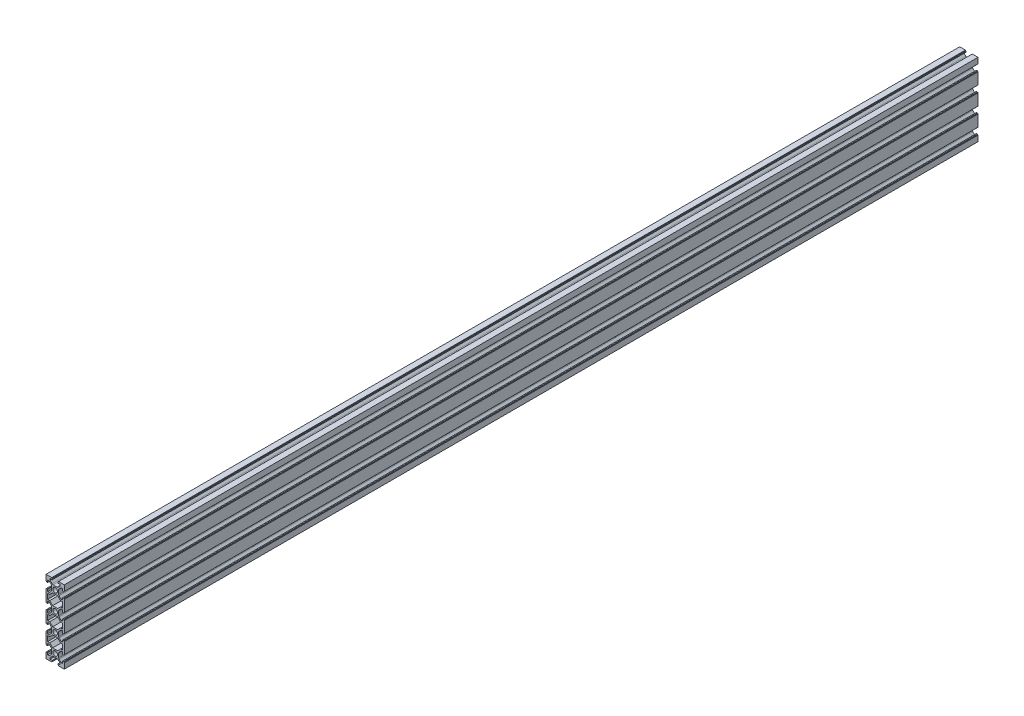
SolidWorks part; units mm, degrees
material "6063 T5"
ref_plane "Спереди" through (0, 0, 0) normal (0, 0, 1) x (1, 0, 0)
ref_plane "Сверху" through (0, 0, 0) normal (0, 1, 0) x (1, 0, 0)
ref_plane "Справа" through (0, 0, 0) normal (1, 0, 0) x (0, 0, -1)
sketch "Эскиз3" plane through (0, 0, 0) normal (0, 0, 1) x (1, 0, 0)
  line L0 (10, 0) -> (10, -20) construction
  line L5 (-10, -5.5) -> (-10, -14.5)
  line L7 (-9.9529, 9.1691) -> (10.0471, 9.1691) construction
  line L8 (-10, 5.5) -> (-10, 10)
  line L9 (-10, 10) -> (-5.5, 10)
  line L10 (5.5, 10) -> (10, 10)
  line L11 (10, 10) -> (10, 5.5)
  line L12 (10, -5.5) -> (10, -14.5)
  line L13 (10, -25.5) -> (10, -34.5)
  line L14 (10, -45.5) -> (10, -54.5)
  line L15 (-10, -25.5) -> (-10, -34.5)
  line L16 (-10, -45.5) -> (-10, -54.5)
  line L17 (-10, -65.5) -> (-10, -70)
  line L18 (-10, -70) -> (-5.5, -70)
  line L20 (5.5, -70) -> (10, -70)
  line L21 (10, -70) -> (10, -65.5)
  line L23 (0, 0) -> (0, -10) construction
  line L24 (0, -10) -> (-10, -10) construction
  line L26 (2.7373, -3.9) -> (-2.7373, -3.9)
  line L27 (-2.7373, -3.9) -> (-5.9373, -7.1)
  line L28 (-5.9373, -7.1) -> (-8.2, -7.1)
  line L29 (-8.2, -7.1) -> (-8.2, -12.9)
  line L31 (5.9373, -7.1) -> (8.2, -7.1)
  line L32 (8.2, -7.1) -> (8.2, -12.9)
  line L33 (2.7373, -3.9) -> (5.9373, -7.1)
  line L35 (-5.9373, -12.9) -> (-8.2, -12.9)
  line L36 (-2.7373, -16.1) -> (-5.9373, -12.9)
  line L37 (2.7373, -16.1) -> (-2.7373, -16.1)
  line L38 (2.7373, -16.1) -> (5.9373, -12.9)
  line L39 (5.9373, -12.9) -> (8.2, -12.9)
  line L41 (-8.2, -27.1) -> (-8.2, -32.9)
  line L42 (-5.9373, -32.9) -> (-8.2, -32.9)
  line L43 (-2.7373, -36.1) -> (-5.9373, -32.9)
  line L44 (2.7373, -36.1) -> (-2.7373, -36.1)
  line L45 (2.7373, -36.1) -> (5.9373, -32.9)
  line L46 (5.9373, -32.9) -> (8.2, -32.9)
  line L47 (8.2, -27.1) -> (8.2, -32.9)
  line L48 (5.9373, -27.1) -> (8.2, -27.1)
  line L49 (2.7373, -23.9) -> (5.9373, -27.1)
  line L50 (2.7373, -23.9) -> (-2.7373, -23.9)
  line L51 (-2.7373, -23.9) -> (-5.9373, -27.1)
  line L52 (-5.9373, -27.1) -> (-8.2, -27.1)
  line L53 (-8.2, -47.1) -> (-8.2, -52.9)
  line L54 (-5.9373, -52.9) -> (-8.2, -52.9)
  line L55 (-2.7373, -56.1) -> (-5.9373, -52.9)
  line L56 (2.7373, -56.1) -> (-2.7373, -56.1)
  line L57 (2.7373, -56.1) -> (5.9373, -52.9)
  line L58 (5.9373, -52.9) -> (8.2, -52.9)
  line L59 (8.2, -47.1) -> (8.2, -52.9)
  line L60 (5.9373, -47.1) -> (8.2, -47.1)
  line L61 (2.7373, -43.9) -> (5.9373, -47.1)
  line L62 (2.7373, -43.9) -> (-2.7373, -43.9)
  line L63 (-2.7373, -43.9) -> (-5.9373, -47.1)
  line L64 (-5.9373, -47.1) -> (-8.2, -47.1)
  line L65 (-8.2, -7.1) -> (-8.2, -27.1) construction
  circle A0 centre (0, 0) radius 2.5
  circle A1 centre (0, -20) radius 2.5
  circle A2 centre (0, -40) radius 2.5
  circle A3 centre (0, -60) radius 2.5
  point P0 (0, 0)
  point P4 (0, 0)
  point P30 (0, 0)
  point P44 (-8.2, -10)
  point P53 (0, -3.9)
  point P57 (8.2, -10)
  line B0 (-8.2, 5.5) -> (-6.6, 5.5)
  line B1 (-6.6, 5.5) -> (-4.3393, 3.2393)
  line B2 (-3.9, 2.1787) -> (-3.9, -2.1787)
  line B3 (-4.3393, -3.2393) -> (-6.6, -5.5)
  line B4 (-6.6, -5.5) -> (-8.2, -5.5)
  line B5 (-8.2, -5.5) -> (-8.2, -3.25)
  line B6 (-8.35, -3.1) -> (-9.35, -3.1)
  line B7 (-9.5, -3.25) -> (-9.5, -3.45)
  line B8 (-9.65, -3.6) -> (-9.85, -3.6)
  line B9 (-9.85, 3.6) -> (-9.65, 3.6)
  line B10 (-9.5, 3.45) -> (-9.5, 3.25)
  line B11 (-9.35, 3.1) -> (-8.35, 3.1)
  line B12 (-8.2, 3.25) -> (-8.2, 5.5)
  line B13 (-10, 3.75) -> (-10, 5.5)
  line B14 (-10, -3.75) -> (-10, -5.5)
  line B15 (-10, 5.5) -> (-10, -5.5) construction
  arc B16 (-8.2, -3.25) -> (-8.35, -3.1) centre (-8.35, -3.25) ccw
  arc B17 (-9.35, -3.1) -> (-9.5, -3.25) centre (-9.35, -3.25) ccw
  arc B18 (-9.5, -3.45) -> (-9.65, -3.6) centre (-9.65, -3.45) cw
  arc B19 (-9.85, -3.6) -> (-10, -3.75) centre (-9.85, -3.75) ccw
  arc B20 (-8.35, 3.1) -> (-8.2, 3.25) centre (-8.35, 3.25) ccw
  arc B21 (-9.5, 3.25) -> (-9.35, 3.1) centre (-9.35, 3.25) ccw
  arc B22 (-9.65, 3.6) -> (-9.5, 3.45) centre (-9.65, 3.45) cw
  arc B23 (-10, 3.75) -> (-9.85, 3.6) centre (-9.85, 3.75) ccw
  arc B24 (-3.9, -2.1787) -> (-4.3393, -3.2393) centre (-5.4, -2.1787) cw
  arc B25 (-4.3393, 3.2393) -> (-3.9, 2.1787) centre (-5.4, 2.1787) cw
  line B26 (8.2, -5.5) -> (6.6, -5.5)
  line B27 (6.6, -5.5) -> (4.3393, -3.2393)
  line B28 (3.9, -2.1787) -> (3.9, 2.1787)
  line B29 (4.3393, 3.2393) -> (6.6, 5.5)
  line B30 (6.6, 5.5) -> (8.2, 5.5)
  line B31 (8.2, 5.5) -> (8.2, 3.25)
  line B32 (8.35, 3.1) -> (9.35, 3.1)
  line B33 (9.5, 3.25) -> (9.5, 3.45)
  line B34 (9.65, 3.6) -> (9.85, 3.6)
  line B35 (9.85, -3.6) -> (9.65, -3.6)
  line B36 (9.5, -3.45) -> (9.5, -3.25)
  line B37 (9.35, -3.1) -> (8.35, -3.1)
  line B38 (8.2, -3.25) -> (8.2, -5.5)
  line B39 (10, -3.75) -> (10, -5.5)
  line B40 (10, 3.75) -> (10, 5.5)
  line B41 (10, -5.5) -> (10, 5.5) construction
  arc B42 (8.2, 3.25) -> (8.35, 3.1) centre (8.35, 3.25) ccw
  arc B43 (9.35, 3.1) -> (9.5, 3.25) centre (9.35, 3.25) ccw
  arc B44 (9.5, 3.45) -> (9.65, 3.6) centre (9.65, 3.45) cw
  arc B45 (9.85, 3.6) -> (10, 3.75) centre (9.85, 3.75) ccw
  arc B46 (8.35, -3.1) -> (8.2, -3.25) centre (8.35, -3.25) ccw
  arc B47 (9.5, -3.25) -> (9.35, -3.1) centre (9.35, -3.25) ccw
  arc B48 (9.65, -3.6) -> (9.5, -3.45) centre (9.65, -3.45) cw
  arc B49 (10, -3.75) -> (9.85, -3.6) centre (9.85, -3.75) ccw
  arc B50 (3.9, 2.1787) -> (4.3393, 3.2393) centre (5.4, 2.1787) cw
  arc B51 (4.3393, -3.2393) -> (3.9, -2.1787) centre (5.4, -2.1787) cw
  line B52 (5.5, 8.2) -> (5.5, 6.6)
  line B53 (5.5, 6.6) -> (3.2393, 4.3393)
  line B54 (2.1787, 3.9) -> (-2.1787, 3.9)
  line B55 (-3.2393, 4.3393) -> (-5.5, 6.6)
  line B56 (-5.5, 6.6) -> (-5.5, 8.2)
  line B57 (-5.5, 8.2) -> (-3.25, 8.2)
  line B58 (-3.1, 8.35) -> (-3.1, 9.35)
  line B59 (-3.25, 9.5) -> (-3.45, 9.5)
  line B60 (-3.6, 9.65) -> (-3.6, 9.85)
  line B61 (3.6, 9.85) -> (3.6, 9.65)
  line B62 (3.45, 9.5) -> (3.25, 9.5)
  line B63 (3.1, 9.35) -> (3.1, 8.35)
  line B64 (3.25, 8.2) -> (5.5, 8.2)
  line B65 (3.75, 10) -> (5.5, 10)
  line B66 (-3.75, 10) -> (-5.5, 10)
  line B67 (5.5, 10) -> (-5.5, 10) construction
  arc B68 (-3.25, 8.2) -> (-3.1, 8.35) centre (-3.25, 8.35) ccw
  arc B69 (-3.1, 9.35) -> (-3.25, 9.5) centre (-3.25, 9.35) ccw
  arc B70 (-3.45, 9.5) -> (-3.6, 9.65) centre (-3.45, 9.65) cw
  arc B71 (-3.6, 9.85) -> (-3.75, 10) centre (-3.75, 9.85) ccw
  arc B72 (3.1, 8.35) -> (3.25, 8.2) centre (3.25, 8.35) ccw
  arc B73 (3.25, 9.5) -> (3.1, 9.35) centre (3.25, 9.35) ccw
  arc B74 (3.6, 9.65) -> (3.45, 9.5) centre (3.45, 9.65) cw
  arc B75 (3.75, 10) -> (3.6, 9.85) centre (3.75, 9.85) ccw
  arc B76 (-2.1787, 3.9) -> (-3.2393, 4.3393) centre (-2.1787, 5.4) cw
  arc B77 (3.2393, 4.3393) -> (2.1787, 3.9) centre (2.1787, 5.4) cw
  line B78 (8.2, -25.5) -> (6.6, -25.5)
  line B79 (6.6, -25.5) -> (4.3393, -23.2393)
  line B80 (3.9, -22.1787) -> (3.9, -17.8213)
  line B81 (4.3393, -16.7607) -> (6.6, -14.5)
  line B82 (6.6, -14.5) -> (8.2, -14.5)
  line B83 (8.2, -14.5) -> (8.2, -16.75)
  line B84 (8.35, -16.9) -> (9.35, -16.9)
  line B85 (9.5, -16.75) -> (9.5, -16.55)
  line B86 (9.65, -16.4) -> (9.85, -16.4)
  line B87 (9.85, -23.6) -> (9.65, -23.6)
  line B88 (9.5, -23.45) -> (9.5, -23.25)
  line B89 (9.35, -23.1) -> (8.35, -23.1)
  line B90 (8.2, -23.25) -> (8.2, -25.5)
  line B91 (10, -23.75) -> (10, -25.5)
  line B92 (10, -16.25) -> (10, -14.5)
  line B93 (10, -25.5) -> (10, -14.5) construction
  arc B94 (8.2, -16.75) -> (8.35, -16.9) centre (8.35, -16.75) ccw
  arc B95 (9.35, -16.9) -> (9.5, -16.75) centre (9.35, -16.75) ccw
  arc B96 (9.5, -16.55) -> (9.65, -16.4) centre (9.65, -16.55) cw
  arc B97 (9.85, -16.4) -> (10, -16.25) centre (9.85, -16.25) ccw
  arc B98 (8.35, -23.1) -> (8.2, -23.25) centre (8.35, -23.25) ccw
  arc B99 (9.5, -23.25) -> (9.35, -23.1) centre (9.35, -23.25) ccw
  arc B100 (9.65, -23.6) -> (9.5, -23.45) centre (9.65, -23.45) cw
  arc B101 (10, -23.75) -> (9.85, -23.6) centre (9.85, -23.75) ccw
  arc B102 (3.9, -17.8213) -> (4.3393, -16.7607) centre (5.4, -17.8213) cw
  arc B103 (4.3393, -23.2393) -> (3.9, -22.1787) centre (5.4, -22.1787) cw
  line B104 (-8.2, -14.5) -> (-6.6, -14.5)
  line B105 (-6.6, -14.5) -> (-4.3393, -16.7607)
  line B106 (-3.9, -17.8213) -> (-3.9, -22.1787)
  line B107 (-4.3393, -23.2393) -> (-6.6, -25.5)
  line B108 (-6.6, -25.5) -> (-8.2, -25.5)
  line B109 (-8.2, -25.5) -> (-8.2, -23.25)
  line B110 (-8.35, -23.1) -> (-9.35, -23.1)
  line B111 (-9.5, -23.25) -> (-9.5, -23.45)
  line B112 (-9.65, -23.6) -> (-9.85, -23.6)
  line B113 (-9.85, -16.4) -> (-9.65, -16.4)
  line B114 (-9.5, -16.55) -> (-9.5, -16.75)
  line B115 (-9.35, -16.9) -> (-8.35, -16.9)
  line B116 (-8.2, -16.75) -> (-8.2, -14.5)
  line B117 (-10, -16.25) -> (-10, -14.5)
  line B118 (-10, -23.75) -> (-10, -25.5)
  line B119 (-10, -14.5) -> (-10, -25.5) construction
  arc B120 (-8.2, -23.25) -> (-8.35, -23.1) centre (-8.35, -23.25) ccw
  arc B121 (-9.35, -23.1) -> (-9.5, -23.25) centre (-9.35, -23.25) ccw
  arc B122 (-9.5, -23.45) -> (-9.65, -23.6) centre (-9.65, -23.45) cw
  arc B123 (-9.85, -23.6) -> (-10, -23.75) centre (-9.85, -23.75) ccw
  arc B124 (-8.35, -16.9) -> (-8.2, -16.75) centre (-8.35, -16.75) ccw
  arc B125 (-9.5, -16.75) -> (-9.35, -16.9) centre (-9.35, -16.75) ccw
  arc B126 (-9.65, -16.4) -> (-9.5, -16.55) centre (-9.65, -16.55) cw
  arc B127 (-10, -16.25) -> (-9.85, -16.4) centre (-9.85, -16.25) ccw
  arc B128 (-3.9, -22.1787) -> (-4.3393, -23.2393) centre (-5.4, -22.1787) cw
  arc B129 (-4.3393, -16.7607) -> (-3.9, -17.8213) centre (-5.4, -17.8213) cw
  line B130 (8.2, -45.5) -> (6.6, -45.5)
  line B131 (6.6, -45.5) -> (4.3393, -43.2393)
  line B132 (3.9, -42.1787) -> (3.9, -37.8213)
  line B133 (4.3393, -36.7607) -> (6.6, -34.5)
  line B134 (6.6, -34.5) -> (8.2, -34.5)
  line B135 (8.2, -34.5) -> (8.2, -36.75)
  line B136 (8.35, -36.9) -> (9.35, -36.9)
  line B137 (9.5, -36.75) -> (9.5, -36.55)
  line B138 (9.65, -36.4) -> (9.85, -36.4)
  line B139 (9.85, -43.6) -> (9.65, -43.6)
  line B140 (9.5, -43.45) -> (9.5, -43.25)
  line B141 (9.35, -43.1) -> (8.35, -43.1)
  line B142 (8.2, -43.25) -> (8.2, -45.5)
  line B143 (10, -43.75) -> (10, -45.5)
  line B144 (10, -36.25) -> (10, -34.5)
  line B145 (10, -45.5) -> (10, -34.5) construction
  arc B146 (8.2, -36.75) -> (8.35, -36.9) centre (8.35, -36.75) ccw
  arc B147 (9.35, -36.9) -> (9.5, -36.75) centre (9.35, -36.75) ccw
  arc B148 (9.5, -36.55) -> (9.65, -36.4) centre (9.65, -36.55) cw
  arc B149 (9.85, -36.4) -> (10, -36.25) centre (9.85, -36.25) ccw
  arc B150 (8.35, -43.1) -> (8.2, -43.25) centre (8.35, -43.25) ccw
  arc B151 (9.5, -43.25) -> (9.35, -43.1) centre (9.35, -43.25) ccw
  arc B152 (9.65, -43.6) -> (9.5, -43.45) centre (9.65, -43.45) cw
  arc B153 (10, -43.75) -> (9.85, -43.6) centre (9.85, -43.75) ccw
  arc B154 (3.9, -37.8213) -> (4.3393, -36.7607) centre (5.4, -37.8213) cw
  arc B155 (4.3393, -43.2393) -> (3.9, -42.1787) centre (5.4, -42.1787) cw
  line B156 (-8.2, -34.5) -> (-6.6, -34.5)
  line B157 (-6.6, -34.5) -> (-4.3393, -36.7607)
  line B158 (-3.9, -37.8213) -> (-3.9, -42.1787)
  line B159 (-4.3393, -43.2393) -> (-6.6, -45.5)
  line B160 (-6.6, -45.5) -> (-8.2, -45.5)
  line B161 (-8.2, -45.5) -> (-8.2, -43.25)
  line B162 (-8.35, -43.1) -> (-9.35, -43.1)
  line B163 (-9.5, -43.25) -> (-9.5, -43.45)
  line B164 (-9.65, -43.6) -> (-9.85, -43.6)
  line B165 (-9.85, -36.4) -> (-9.65, -36.4)
  line B166 (-9.5, -36.55) -> (-9.5, -36.75)
  line B167 (-9.35, -36.9) -> (-8.35, -36.9)
  line B168 (-8.2, -36.75) -> (-8.2, -34.5)
  line B169 (-10, -36.25) -> (-10, -34.5)
  line B170 (-10, -43.75) -> (-10, -45.5)
  line B171 (-10, -34.5) -> (-10, -45.5) construction
  arc B172 (-8.2, -43.25) -> (-8.35, -43.1) centre (-8.35, -43.25) ccw
  arc B173 (-9.35, -43.1) -> (-9.5, -43.25) centre (-9.35, -43.25) ccw
  arc B174 (-9.5, -43.45) -> (-9.65, -43.6) centre (-9.65, -43.45) cw
  arc B175 (-9.85, -43.6) -> (-10, -43.75) centre (-9.85, -43.75) ccw
  arc B176 (-8.35, -36.9) -> (-8.2, -36.75) centre (-8.35, -36.75) ccw
  arc B177 (-9.5, -36.75) -> (-9.35, -36.9) centre (-9.35, -36.75) ccw
  arc B178 (-9.65, -36.4) -> (-9.5, -36.55) centre (-9.65, -36.55) cw
  arc B179 (-10, -36.25) -> (-9.85, -36.4) centre (-9.85, -36.25) ccw
  arc B180 (-3.9, -42.1787) -> (-4.3393, -43.2393) centre (-5.4, -42.1787) cw
  arc B181 (-4.3393, -36.7607) -> (-3.9, -37.8213) centre (-5.4, -37.8213) cw
  line B182 (8.2, -65.5) -> (6.6, -65.5)
  line B183 (6.6, -65.5) -> (4.3393, -63.2393)
  line B184 (3.9, -62.1787) -> (3.9, -57.8213)
  line B185 (4.3393, -56.7607) -> (6.6, -54.5)
  line B186 (6.6, -54.5) -> (8.2, -54.5)
  line B187 (8.2, -54.5) -> (8.2, -56.75)
  line B188 (8.35, -56.9) -> (9.35, -56.9)
  line B189 (9.5, -56.75) -> (9.5, -56.55)
  line B190 (9.65, -56.4) -> (9.85, -56.4)
  line B191 (9.85, -63.6) -> (9.65, -63.6)
  line B192 (9.5, -63.45) -> (9.5, -63.25)
  line B193 (9.35, -63.1) -> (8.35, -63.1)
  line B194 (8.2, -63.25) -> (8.2, -65.5)
  line B195 (10, -63.75) -> (10, -65.5)
  line B196 (10, -56.25) -> (10, -54.5)
  line B197 (10, -65.5) -> (10, -54.5) construction
  arc B198 (8.2, -56.75) -> (8.35, -56.9) centre (8.35, -56.75) ccw
  arc B199 (9.35, -56.9) -> (9.5, -56.75) centre (9.35, -56.75) ccw
  arc B200 (9.5, -56.55) -> (9.65, -56.4) centre (9.65, -56.55) cw
  arc B201 (9.85, -56.4) -> (10, -56.25) centre (9.85, -56.25) ccw
  arc B202 (8.35, -63.1) -> (8.2, -63.25) centre (8.35, -63.25) ccw
  arc B203 (9.5, -63.25) -> (9.35, -63.1) centre (9.35, -63.25) ccw
  arc B204 (9.65, -63.6) -> (9.5, -63.45) centre (9.65, -63.45) cw
  arc B205 (10, -63.75) -> (9.85, -63.6) centre (9.85, -63.75) ccw
  arc B206 (3.9, -57.8213) -> (4.3393, -56.7607) centre (5.4, -57.8213) cw
  arc B207 (4.3393, -63.2393) -> (3.9, -62.1787) centre (5.4, -62.1787) cw
  line B208 (-8.2, -54.5) -> (-6.6, -54.5)
  line B209 (-6.6, -54.5) -> (-4.3393, -56.7607)
  line B210 (-3.9, -57.8213) -> (-3.9, -62.1787)
  line B211 (-4.3393, -63.2393) -> (-6.6, -65.5)
  line B212 (-6.6, -65.5) -> (-8.2, -65.5)
  line B213 (-8.2, -65.5) -> (-8.2, -63.25)
  line B214 (-8.35, -63.1) -> (-9.35, -63.1)
  line B215 (-9.5, -63.25) -> (-9.5, -63.45)
  line B216 (-9.65, -63.6) -> (-9.85, -63.6)
  line B217 (-9.85, -56.4) -> (-9.65, -56.4)
  line B218 (-9.5, -56.55) -> (-9.5, -56.75)
  line B219 (-9.35, -56.9) -> (-8.35, -56.9)
  line B220 (-8.2, -56.75) -> (-8.2, -54.5)
  line B221 (-10, -56.25) -> (-10, -54.5)
  line B222 (-10, -63.75) -> (-10, -65.5)
  line B223 (-10, -54.5) -> (-10, -65.5) construction
  arc B224 (-8.2, -63.25) -> (-8.35, -63.1) centre (-8.35, -63.25) ccw
  arc B225 (-9.35, -63.1) -> (-9.5, -63.25) centre (-9.35, -63.25) ccw
  arc B226 (-9.5, -63.45) -> (-9.65, -63.6) centre (-9.65, -63.45) cw
  arc B227 (-9.85, -63.6) -> (-10, -63.75) centre (-9.85, -63.75) ccw
  arc B228 (-8.35, -56.9) -> (-8.2, -56.75) centre (-8.35, -56.75) ccw
  arc B229 (-9.5, -56.75) -> (-9.35, -56.9) centre (-9.35, -56.75) ccw
  arc B230 (-9.65, -56.4) -> (-9.5, -56.55) centre (-9.65, -56.55) cw
  arc B231 (-10, -56.25) -> (-9.85, -56.4) centre (-9.85, -56.25) ccw
  arc B232 (-3.9, -62.1787) -> (-4.3393, -63.2393) centre (-5.4, -62.1787) cw
  arc B233 (-4.3393, -56.7607) -> (-3.9, -57.8213) centre (-5.4, -57.8213) cw
  line B234 (-5.5, -68.2) -> (-5.5, -66.6)
  line B235 (-5.5, -66.6) -> (-3.2393, -64.3393)
  line B236 (-2.1787, -63.9) -> (2.1787, -63.9)
  line B237 (3.2393, -64.3393) -> (5.5, -66.6)
  line B238 (5.5, -66.6) -> (5.5, -68.2)
  line B239 (5.5, -68.2) -> (3.25, -68.2)
  line B240 (3.1, -68.35) -> (3.1, -69.35)
  line B241 (3.25, -69.5) -> (3.45, -69.5)
  line B242 (3.6, -69.65) -> (3.6, -69.85)
  line B243 (-3.6, -69.85) -> (-3.6, -69.65)
  line B244 (-3.45, -69.5) -> (-3.25, -69.5)
  line B245 (-3.1, -69.35) -> (-3.1, -68.35)
  line B246 (-3.25, -68.2) -> (-5.5, -68.2)
  line B247 (-3.75, -70) -> (-5.5, -70)
  line B248 (3.75, -70) -> (5.5, -70)
  line B249 (-5.5, -70) -> (5.5, -70) construction
  arc B250 (3.25, -68.2) -> (3.1, -68.35) centre (3.25, -68.35) ccw
  arc B251 (3.1, -69.35) -> (3.25, -69.5) centre (3.25, -69.35) ccw
  arc B252 (3.45, -69.5) -> (3.6, -69.65) centre (3.45, -69.65) cw
  arc B253 (3.6, -69.85) -> (3.75, -70) centre (3.75, -69.85) ccw
  arc B254 (-3.1, -68.35) -> (-3.25, -68.2) centre (-3.25, -68.35) ccw
  arc B255 (-3.25, -69.5) -> (-3.1, -69.35) centre (-3.25, -69.35) ccw
  arc B256 (-3.6, -69.65) -> (-3.45, -69.5) centre (-3.45, -69.65) cw
  arc B257 (-3.75, -70) -> (-3.6, -69.85) centre (-3.75, -69.85) ccw
  arc B258 (2.1787, -63.9) -> (3.2393, -64.3393) centre (2.1787, -65.4) cw
  arc B259 (-3.2393, -64.3393) -> (-2.1787, -63.9) centre (-2.1787, -65.4) cw
  dimension "D3" = 10
  dimension "D5" = 10
  dimension "D6" = 4
  dimension "D1" = 5
  dimension "D2" = 10
  dimension "D4" = 20
  dimension "D7" = 20
  dimension "D8" = 10
  dimension "D9" = 1.6
  dimension "D10" = 1.6
  dimension "D11" = 3.9
  dimension "D12" = 3
  dimension "D13" = 20
sketch_block_instance "6B-1"
sketch_block "Блок2" parameters "D5"=0.15, "D6"=1.5, "D1"=11, "D2"=1.6, "D3"=135, "D4"=7.2
sketch_block_instance "Блок2-25"
sketch_block_instance "Блок2-26"
sketch_block_instance "Блок2-27"
sketch_block_instance "Блок2-28"
sketch_block_instance "Блок2-29"
sketch_block_instance "Блок2-30"
sketch_block_instance "Блок2-31"
sketch_block_instance "Блок2-32"
sketch_block_instance "Блок2-33"
extrude "Бобышка-Вытянуть1" add sketch "Эскиз3" along normal blind 1000
